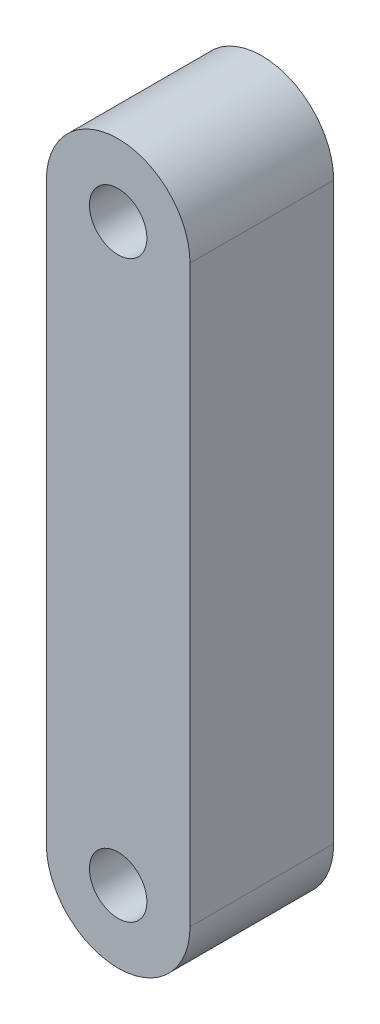
SolidWorks part; units mm, degrees
ref_plane "Alzado" through (0, 0, 0) normal (0, 0, 1) x (1, 0, 0)
ref_plane "Planta" through (0, 0, 0) normal (0, 1, 0) x (1, 0, 0)
ref_plane "Vista lateral" through (0, 0, 0) normal (1, 0, 0) x (0, 0, -1)
sketch "Croquis1" plane through (0, 0, 0) normal (0, 0, 1) x (1, 0, 0)
  line L0 (0, 0) -> (0, 40) construction
  line L1 (-5, 40) -> (-5, 0)
  line L3 (5, 0) -> (5, 40)
  circle A0 centre (0, 0) radius 2
  arc A1 (-5, 0) -> (5, 0) centre (0, 0) ccw
  circle A2 centre (0, 40) radius 2
  arc A3 (5, 40) -> (-5, 40) centre (0, 40) ccw
extrude "Saliente-Extruir1" add sketch "Croquis1" along normal blind 10
